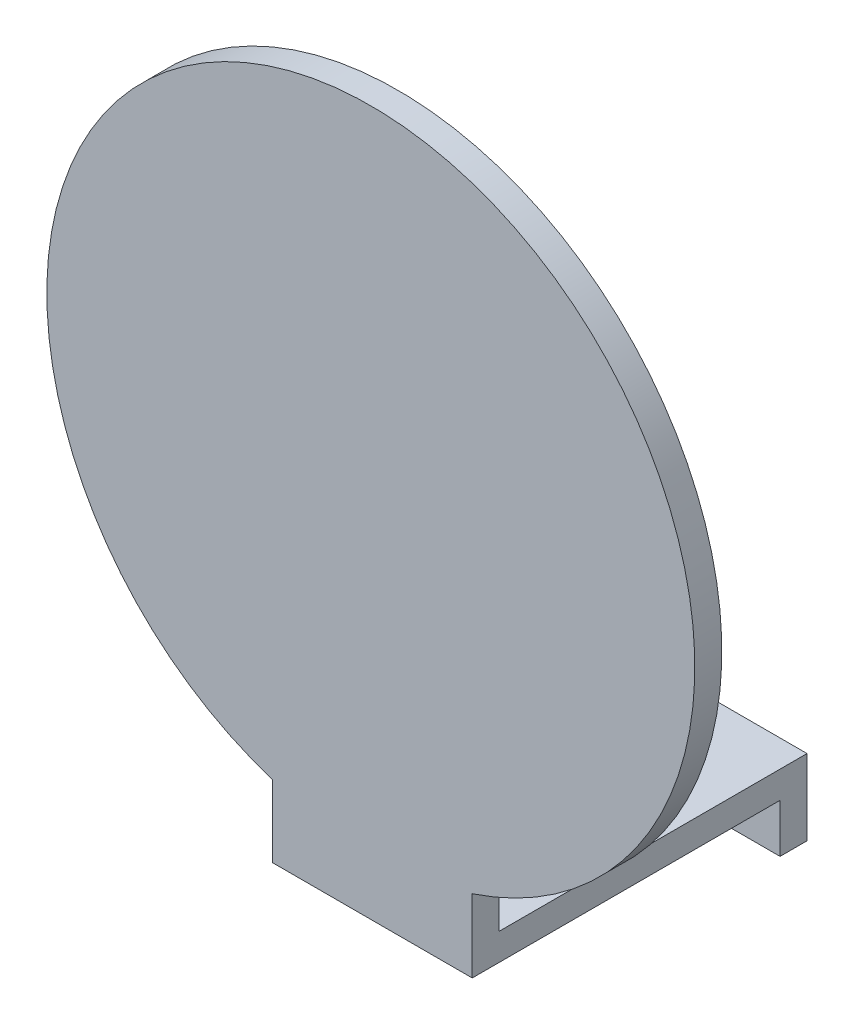
SolidWorks part; units mm, degrees
ref_plane "Front Plane" through (0, 0, 0) normal (0, 0, 1) x (1, 0, 0)
ref_plane "Top Plane" through (0, 0, 0) normal (0, 1, 0) x (1, 0, 0)
ref_plane "Right Plane" through (0, 0, 0) normal (1, 0, 0) x (0, 0, -1)
ref_plane "Plane1" through (0, 0, 0) normal (0, 0, 1) x (1, 0, 0)
sketch "Sketch2" plane through (0, 0, -2347.0183) normal (0, 0, 1) x (1, 0, 0)
  line L0 (-18.5, 5) -> (18.5, 5)
  line L1 (-18.5, 5) -> (-18.5, -3)
  line L2 (18.5, 5) -> (18.5, -3)
  line L3 (-18.5, -3) -> (18.5, -3)
  circle A0 centre (10, 1) radius 2.1
  circle A2 centre (-10, 1) radius 2.1
  dimension "D2" = 8.5
  dimension "D4" = 4.2
  dimension "D7" = 4.2
  dimension "D1" = 8
  dimension "D3" = 4
  dimension "D5" = 8.5
  dimension "D6" = 4
  dimension "D8" = 37
extrude "Boss-Extrude1" add sketch "Sketch2" along normal blind 5
sketch "Sketch3" plane through (0, 5, 0) normal (0, 1, 0) x (1, 0, 0)
  line L0 (18.5, 2342.0183) -> (-18.5, 2342.0183)
  line L1 (18.5, 2342.0183) -> (18.5, 2347.0183)
  line L2 (-18.5, 2342.0183) -> (-18.5, 2347.0183)
  line L3 (18.5, 2347.0183) -> (-18.5, 2347.0183)
extrude "Boss-Extrude2" add sketch "Sketch3" along normal blind 6
sketch "Sketch4" plane through (0, 0, -2342.0183) normal (0, 0, 1) x (1, 0, 0)
  line L0 (18.5, 11) -> (-18.5, 11)
  line L1 (18.5, 11) -> (18.5, 6)
  line L2 (-18.5, 11) -> (-18.5, 6)
  line L3 (18.5, 6) -> (-18.5, 6)
  line L4 (-18.5, 11) -> (-18.5, -3) construction
  dimension "D1" = 5
extrude "Boss-Extrude3" add sketch "Sketch4" along normal blind 57
sketch "Sketch5" plane through (0, 11, 0) normal (0, 1, 0) x (1, 0, 0)
  line L0 (18.5, 2285.0183) -> (-18.5, 2285.0183)
  line L1 (18.5, 2285.0183) -> (18.5, 2290.0183)
  line L2 (-18.5, 2285.0183) -> (-18.5, 2290.0183)
  line L3 (18.5, 2290.0183) -> (-18.5, 2290.0183)
  line L4 (-18.5, 2347.0183) -> (-18.5, 2285.0183) construction
  dimension "D1" = 5
extrude "Boss-Extrude4" add sketch "Sketch5" along normal blind 27.5
sketch "Sketch6" plane through (0, 0, -2285.0183) normal (0, 0, 1) x (1, 0, 0)
  line L1 (18.5, 6) -> (18.5, 38.5) construction
  circle A0 centre (-0.2794, 76.5) radius 60
  dimension "D1" = 120
  dimension "D2" = 76.5
  dimension "D3" = 18.7794
extrude "Boss-Extrude5" add sketch "Sketch6" against normal blind 5
